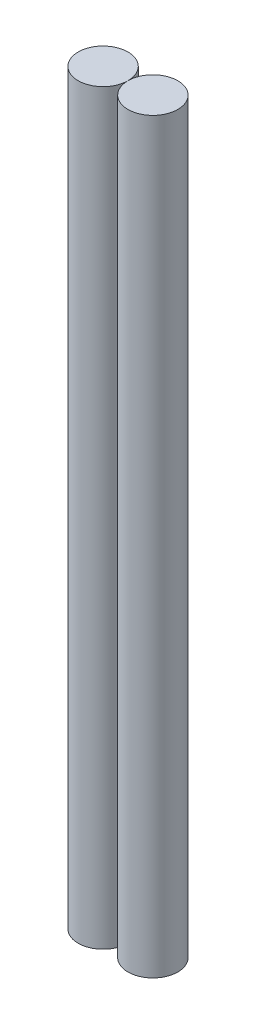
SolidWorks part; units mm, degrees
ref_plane "Front Plane" through (0, 0, 0) normal (0, 0, 1) x (1, 0, 0)
ref_plane "Top Plane" through (0, 0, 0) normal (0, 1, 0) x (1, 0, 0)
ref_plane "Right Plane" through (0, 0, 0) normal (1, 0, 0) x (0, 0, -1)
sketch "Sketch1" plane through (0, 0, 0) normal (0, 1, 0) x (1, 0, 0)
  line L0 (0, 0) -> (18, 0) construction
  circle A0 centre (0, 0) radius 9
  circle A1 centre (18, 0) radius 9
  point P5 (19.8036, 0)
  dimension "D1" = 18
extrude "Boss-Extrude1" add sketch "Sketch1" along normal blind 270
